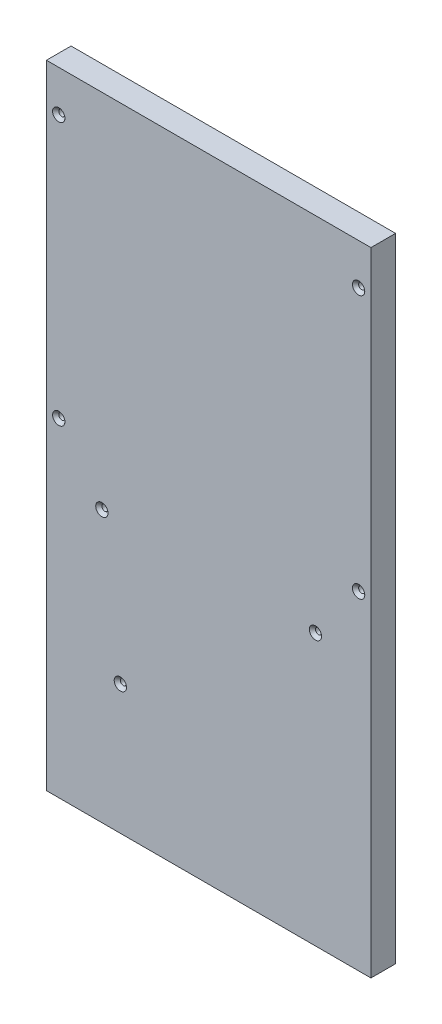
SolidWorks part; units mm, degrees
ref_plane "Front Plane" through (0, 0, 0) normal (0, 0, 1) x (1, 0, 0)
ref_plane "Top Plane" through (0, 0, 0) normal (0, 1, 0) x (1, 0, 0)
ref_plane "Right Plane" through (0, 0, 0) normal (1, 0, 0) x (0, 0, -1)
sketch "Sketch1" plane through (0, 0, 0) normal (0, 0, 1) x (1, 0, 0)
  line L0 (-164.9512, -64.4634) -> (-6.9512, -64.4634) construction
  line L1 (-164.9512, 111.5366) -> (-6.9512, 111.5366)
  line L2 (-164.9512, 111.5366) -> (-164.9512, -196.4634)
  line L3 (-164.9512, -196.4634) -> (-6.9512, -196.4634)
  line L4 (-6.9512, 111.5366) -> (-6.9512, -196.4634)
  circle A0 centre (-137.9512, -64.4634) radius 1.5
  circle A1 centre (-33.9512, -64.4634) radius 1.5
  circle A2 centre (-128.9512, -133.4634) radius 1.5
  circle A3 centre (-158.9512, 91.5366) radius 1.5
  circle A4 centre (-158.9512, -36.4634) radius 1.5
  circle A5 centre (-12.9512, 91.5366) radius 1.5
  circle A6 centre (-12.9512, -36.4634) radius 1.5
  dimension "D6" = 3
  dimension "D7" = 3
  dimension "D10" = 3
  dimension "D13" = 3
  dimension "D14" = 3
  dimension "D17" = 3
  dimension "D18" = 3
  dimension "D1" = 308
  dimension "D2" = 158
  dimension "D3" = 132
  dimension "D4" = 27
  dimension "D5" = 27
  dimension "D8" = 63
  dimension "D9" = 122
  dimension "D11" = 6
  dimension "D12" = 6
  dimension "D15" = 20
  dimension "D16" = 148
  dimension "D19" = 6
  dimension "D20" = 6
  dimension "D21" = 148
  dimension "D22" = 20
extrude "Boss-Extrude1" add sketch "Sketch1" along normal blind 12
sketch "Sketch4" plane through (0, 0, 0) normal (0, 1, 0) x (1, 0, 0)
  line L0 (-164.9512, -6) -> (-6.9512, -6) construction
  line L1 (-164.9512, -12) -> (-164.9512, 0) construction
  line L2 (-6.9512, -12) -> (-6.9512, 0) construction
  circle A0 centre (-149.9512, -6) radius 1.5
  circle A1 centre (-21.9512, -6) radius 1.5
  dimension "D3" = 3
  dimension "D4" = 3
  dimension "D1" = 15
  dimension "D2" = 15
extrude "Cut-Extrude3" cut sketch "Sketch4" along normal blind 20 from surface at -196.4634 starting at face at (-85.9512, -196.4634, 6)
sketch "Sketch5" plane through (0, 0, 0) normal (0, 0, 1) x (1, 0, 0)
  circle A0 centre (-137.9512, -64.4634) radius 3
  circle A1 centre (-33.9512, -64.4634) radius 3
  circle A2 centre (-128.9512, -133.4634) radius 3
  circle A3 centre (-158.9512, 91.5366) radius 3
  circle A4 centre (-158.9512, -36.4634) radius 3
  circle A5 centre (-12.9512, 91.5366) radius 3
  circle A6 centre (-12.9512, -36.4634) radius 3
  dimension "D1" = 6
  dimension "D2" = 6
  dimension "D3" = 6
  dimension "D4" = 6
  dimension "D5" = 6
  dimension "D6" = 6
  dimension "D7" = 6
extrude "Cut-Extrude4" cut sketch "Sketch5" against normal blind 3 draft 45 from surface at 12
sketch "Sketch6" plane through (0, 0, 0) normal (0, 0, 1) x (1, 0, 0)
  circle A0 centre (-45.9512, -31.4634) radius 7
  dimension "D1" = 14
  dimension "D2" = 39
  dimension "D3" = 165
extrude "Cut-Extrude5" cut sketch "Sketch6" along normal blind 5 from surface at 0 starting at face at (-85.9512, -42.4634, 0)
